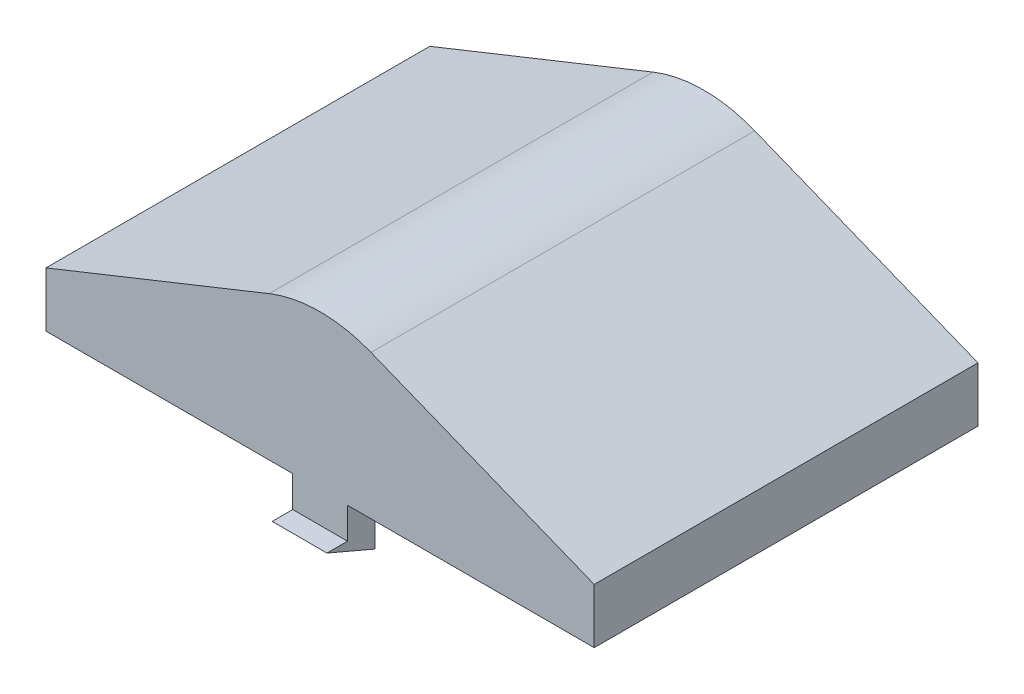
SolidWorks part; units mm, degrees
ref_plane "Front Plane" through (0, 0, 0) normal (0, 0, 1) x (1, 0, 0)
ref_plane "Top Plane" through (0, 0, 0) normal (0, 1, 0) x (1, 0, 0)
ref_plane "Right Plane" through (0, 0, 0) normal (1, 0, 0) x (0, 0, -1)
sketch "Sketch1" plane through (0, 0, 0) normal (0, 0, 1) x (1, 0, 0)
  line L0 (-10, 0) -> (10, 0)
  line L1 (10, 0) -> (10, 2)
  line L2 (10, 2) -> (0, 6)
  line L3 (0, 6) -> (0, 0) construction
  line L4 (-10, 2) -> (0, 6)
  line L5 (-10, 0) -> (-10, 2)
  dimension "D1" = 10
  dimension "D2" = 6
  dimension "D3" = 2
extrude "Extrude1" add sketch "Sketch1" along normal mid plane 14
fillet "Fillet1" radius 5 1 edges at (0, 6, 0)
shell "Shell1" thickness 1
sketch "Sketch2" plane through (0, 0, 0) normal (1, 0, 0) x (0, 0, -1)
  line L0 (-7, 0) -> (-7, 2) construction
  line L1 (-6, 0) -> (-7, 0)
  line L2 (-6, 0) -> (-6, -1.8852)
  line L3 (7, 5.6148) -> (-7, 5.6148) construction
  line L4 (-7, 0) -> (-7, -1.1352)
  line L5 (-6, -1.8852) -> (-7.75, -1.1352)
  line L6 (-7.75, -1.1352) -> (-7, -1.1352)
  dimension "D1" = 7.5
  dimension "D2" = 6.75
  dimension "D3" = 1.75
extrude "Extrude2" add sketch "Sketch2" along normal mid plane 2
mirror "Mirror1" about plane through (0, 0, 0) normal (0, 0, 1) of "Extrude2"
